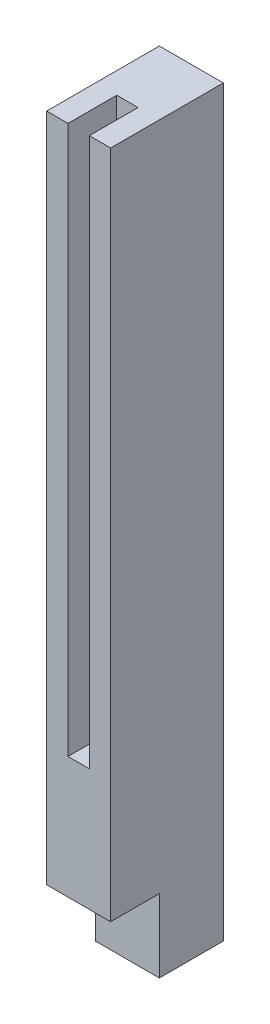
SolidWorks part; units mm, degrees
ref_plane "Front Plane" through (0, 0, 0) normal (0, 0, 1) x (1, 0, 0)
ref_plane "Top Plane" through (0, 0, 0) normal (0, 1, 0) x (1, 0, 0)
ref_plane "Right Plane" through (0, 0, 0) normal (1, 0, 0) x (0, 0, -1)
sketch "Sketch1" plane through (0, 0, 0) normal (0, 1, 0) x (1, 0, 0)
  line L1 (-2.625, -2.625) -> (2.625, -2.625)
  line L2 (-2.625, -2.625) -> (-2.625, 2.625)
  line L3 (-2.625, 2.625) -> (2.625, 2.625)
  line L4 (2.625, -2.625) -> (2.625, 2.625)
  line L5 (-2.625, -2.625) -> (2.625, 2.625) construction
  line L6 (-2.625, 2.625) -> (2.625, -2.625) construction
  point P0 (0, 0)
  dimension "D1" = 5.25
  dimension "D2" = 5.25
extrude "Boss-Extrude1" add sketch "Sketch1" along normal blind 6
sketch "Sketch2" plane through (0, 6, 0) normal (0, 1, 0) x (1, 0, 0)
  line L1 (-2.625, 2.625) -> (2.625, 2.625)
  line L2 (-2.625, 2.625) -> (-2.625, -6.625)
  line L3 (-2.625, -6.625) -> (2.625, -6.625)
  line L4 (2.625, 2.625) -> (2.625, -6.625)
  dimension "D1" = 5.25
  dimension "D2" = 9.25
extrude "Boss-Extrude2" add sketch "Sketch2" along normal blind 55
sketch "Sketch3" plane through (0, 61, 0) normal (0, 1, 0) x (1, 0, 0)
  line L0 (-2.625, -6.625) -> (2.625, -6.625) construction
  line L1 (-0.875, -10.625) -> (0.875, -10.625)
  line L2 (-0.875, -10.625) -> (-0.875, -2.625)
  line L3 (-0.875, -2.625) -> (0.875, -2.625)
  line L4 (0.875, -10.625) -> (0.875, -2.625)
  line L5 (-0.875, -10.625) -> (0.875, -2.625) construction
  line L6 (-0.875, -2.625) -> (0.875, -10.625) construction
  point P0 (0, -6.625)
  dimension "D1" = 1.75
  dimension "D2" = 4
extrude "Cut-Extrude1" cut sketch "Sketch3" against normal blind 45
